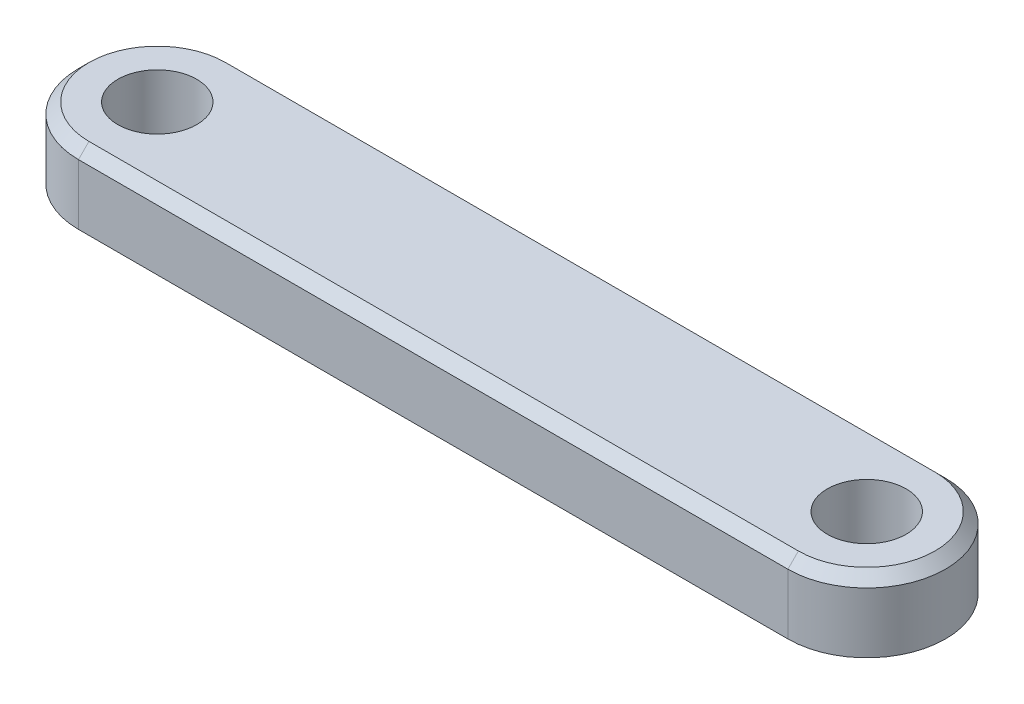
SolidWorks part; units mm, degrees
ref_plane "Front Plane" through (0, 0, 0) normal (0, 0, 1) x (1, 0, 0)
ref_plane "Top Plane" through (0, 0, 0) normal (0, 1, 0) x (1, 0, 0)
ref_plane "Right Plane" through (0, 0, 0) normal (1, 0, 0) x (0, 0, -1)
sketch "Sketch1" plane through (0, 0, 0) normal (0, 1, 0) x (1, 0, 0)
  line L0 (-18.0944, 0) -> (24.4801, 0) construction
  line L1 (-13.5, 0) -> (13.5, 0) construction
  line L2 (-13.5, 3) -> (13.5, 3)
  line L3 (-13.5, -3) -> (13.5, -3)
  line L4 (0, 10.1131) -> (0, -14.786) construction
  arc A0 (-13.5, 3) -> (-13.5, -3) centre (-13.5, 0) ccw
  arc A1 (13.5, -3) -> (13.5, 3) centre (13.5, 0) ccw
  circle A2 centre (-13.5, 0) radius 1.5
  circle A4 centre (13.5, 0) radius 1.5
  point P5 (0, 0)
  point P11 (-16.5, 0)
  point P12 (16.5, 0)
  dimension "D3" = 3
  dimension "D1" = 6
  dimension "D2" = 33
extrude "Boss-Extrude1" add sketch "Sketch1" along normal mid plane 2.7
chamfer "Chamfer1" distance 0.4 angle 45 4 edges at (16.5, 1.35, 0) (0, 1.35, -3) (-16.5, 1.35, 0) (0, 1.35, 3)
